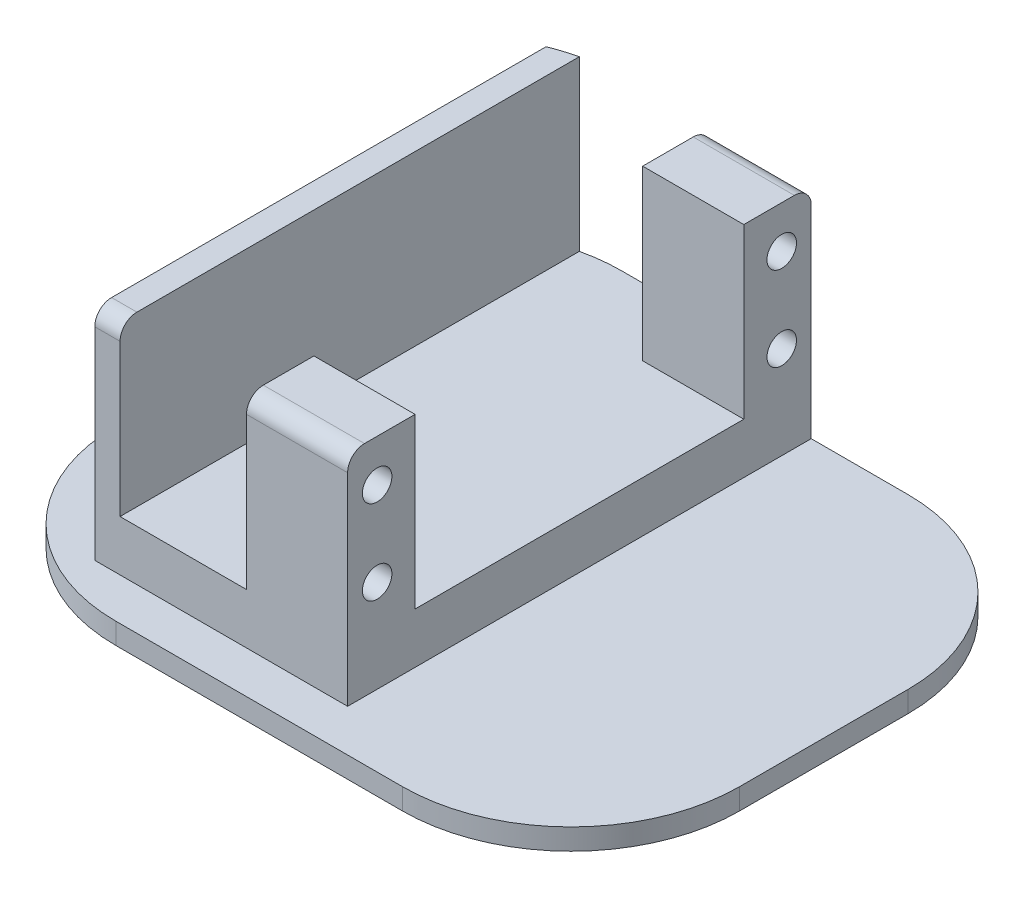
SolidWorks part; units mm, degrees
ref_plane "Plan de face" through (0, 0, 0) normal (0, 0, 1) x (1, 0, 0)
ref_plane "Plan de dessus" through (0, 0, 0) normal (0, 1, 0) x (1, 0, 0)
ref_plane "Plan de droite" through (0, 0, 0) normal (1, 0, 0) x (0, 0, -1)
sketch "Esquisse1" plane through (0, 0, 0) normal (0, 1, 0) x (1, 0, 0)
  line L1 (0, 0) -> (74, 0)
  line L2 (0, 0) -> (0, 60)
  line L3 (0, 60) -> (74, 60)
  line L4 (74, 0) -> (74, 60)
  dimension "D1" = 60
  dimension "D2" = 74
extrude "Boss.-Extru.1" add sketch "Esquisse1" along normal blind 2.5
sketch "Esquisse2" plane through (0, 2.5, 0) normal (0, 1, 0) x (1, 0, 0)
  line L1 (12.5, 60) -> (42.5, 60)
  line L2 (12.5, 60) -> (12.5, 5)
  line L3 (12.5, 5) -> (42.5, 5)
  line L4 (42.5, 60) -> (42.5, 5)
  line L5 (74, 60) -> (0, 60) construction
  line L6 (0, 60) -> (0, 0) construction
  dimension "D1" = 30
  dimension "D2" = 55
  dimension "D4" = 12.5
extrude "Boss.-Extru.2" add sketch "Esquisse2" along normal blind 6
sketch "Esquisse4" plane through (0, 8.5, 0) normal (0, 1, 0) x (1, 0, 0)
  line L0 (42.5, 5) -> (42.5, 60) construction
  line L1 (42.5, 60) -> (30.5, 60)
  line L2 (42.5, 60) -> (42.5, 52)
  line L3 (42.5, 52) -> (30.5, 52)
  line L4 (12.5, 60) -> (12.5, 52)
  line L5 (12.5, 60) -> (12.5, 5) construction
  line L7 (12.5, 5) -> (15.5, 5)
  line L8 (12.5, 5) -> (12.5, 13)
  line L9 (30.5, 13) -> (42.5, 13)
  line L10 (42.5, 5) -> (42.5, 13)
  line L11 (42.5, 60) -> (12.5, 60) construction
  line L12 (42.5, 5) -> (42.5, 60) construction
  line L13 (15.5, 60) -> (12.5, 60)
  line L14 (12.5, 52) -> (12.5, 13)
  line L15 (30.5, 5) -> (42.5, 5)
  line L16 (15.5, 52) -> (15.5, 13)
  line L17 (15.5, 52) -> (15.5, 60)
  line L19 (30.5, 52) -> (30.5, 60)
  line L20 (15.5, 13) -> (15.5, 5)
  line L22 (30.5, 13) -> (30.5, 5)
  dimension "D1" = 8
  dimension "D2" = 8
  dimension "D3" = 27
  dimension "D4" = 15
  dimension "D5" = 15
extrude "Boss.-Extru.3" add sketch "Esquisse4" along normal blind 20
sketch "Esquisse5" plane through (42.5, 0, 0) normal (1, 0, 0) x (0, 0, -1)
  line L0 (60, 28.5) -> (60, 2.5) construction
  line L1 (5, 28.5) -> (5, 2.5) construction
  line L3 (13, 8.5) -> (52, 8.5) construction
  circle A0 centre (8.5, 23.5) radius 1.75
  circle A1 centre (8.5, 13.5) radius 1.75
  circle A2 centre (56.5, 23.5) radius 1.75
  circle A3 centre (56.5, 13.5) radius 1.75
  point P8 (60, 15.5)
  dimension "D1" = 3.5
  dimension "D2" = 3.5
  dimension "D3" = 3.5
  dimension "D4" = 3.5
  dimension "D5" = 3.5
  dimension "D6" = 3.5
  dimension "D7" = 3.5
  dimension "D8" = 3.5
  dimension "D9" = 3.5
  dimension "D10" = 5
  dimension "D11" = 10
  dimension "D12" = 10
  dimension "D13" = 5
  dimension "D14" = 5
extrude "Enlèv. mat.-Extru.1" cut sketch "Esquisse5" against normal blind 20
sketch "Esquisse6" plane through (12.5, 0, 0) normal (-1, 0, 0) x (0, 0, 1)
  line L0 (-60, 28.5) -> (-5, 28.5) construction
  line L2 (-60, 28.5) -> (-60, 2.5) construction
  circle A0 centre (-42, 18.5) radius 2.95
  dimension "D1" = 5.9
  dimension "D2" = 10
  dimension "D3" = 18
extrude "Boss.-Extru.4" add sketch "Esquisse6" along normal blind 5
fillet "Congé1" radius 1 1 edges at (12.5, 18.5, -44.95)
fillet "Congé2" radius 20 4 edges at (74, 1.25, -60) (74, 1.25, 0) (0, 1.25, 0) (0, 1.25, -60)
fillet "Congé3" radius 2 2 edges at (36.5, 28.5, -60) (36.5, 28.5, -5)
